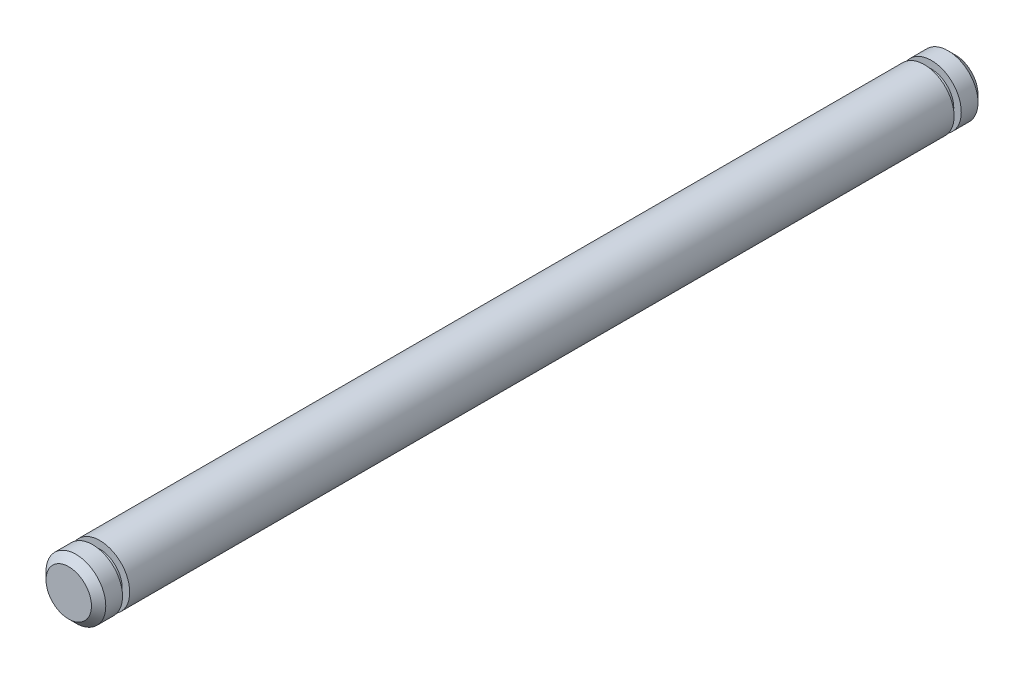
SolidWorks part; units mm, degrees
ref_plane "Front Plane" through (0, 0, 0) normal (0, 0, 1) x (1, 0, 0)
ref_plane "Top Plane" through (0, 0, 0) normal (0, 1, 0) x (1, 0, 0)
ref_plane "Right Plane" through (0, 0, 0) normal (1, 0, 0) x (0, 0, -1)
sketch "Sketch1" plane through (0, 0, 0) normal (0, 0, 1) x (1, 0, 0)
  circle A0 centre (0, 0) radius 1.5875
  dimension "D1" = 3.175
extrude "Boss-Extrude1" add sketch "Sketch1" along normal mid plane 43.7845
sketch "Sketch2" plane through (0, 0, 21.8923) normal (0, 0, 1) x (1, 0, 0)
  circle A0 centre (0, 0) radius 1.1913
  dimension "D1" = 2.3825
extrude "Boss-Extrude2" add sketch "Sketch2" along normal blind 0.381
sketch "Sketch3" plane through (0, 0, 22.2733) normal (0, 0, 1) x (1, 0, 0)
  circle A0 centre (0, 0) radius 1.5875 construction
  circle A1 centre (0, 0) radius 1.5875
extrude "Boss-Extrude3" add sketch "Sketch3" along normal blind 1.27
chamfer "Chamfer1" distance 0.381 1 edges at (1.5875, 0, 23.5433)
mirror "Mirror1" about plane through (0, 0, 0) normal (0, 0, 1) of "Boss-Extrude2", "Chamfer1", "Boss-Extrude3"
